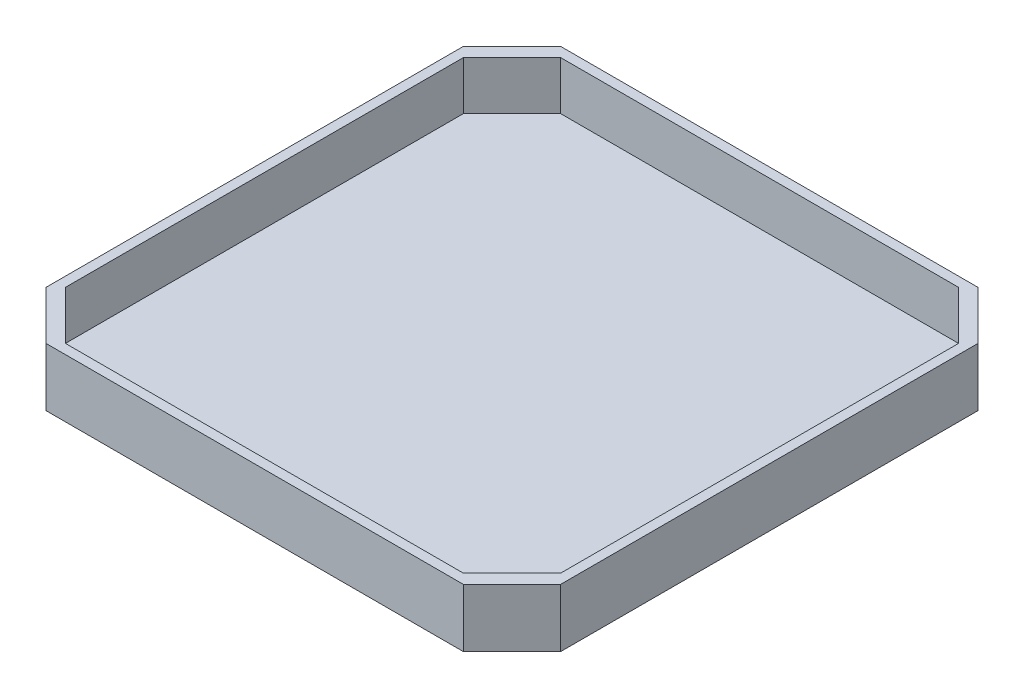
SolidWorks part; units mm, degrees
material "PLA Black"
ref_plane "Front" through (0, 0, 0) normal (0, 0, 1) x (1, 0, 0)
ref_plane "Top" through (0, 0, 0) normal (0, 1, 0) x (1, 0, 0)
ref_plane "Right" through (0, 0, 0) normal (1, 0, 0) x (0, 0, -1)
sketch "Sketch1" plane through (0, 0, 0) normal (0, 1, 0) x (1, 0, 0)
  line L0 (0, 53) -> (0, -53) construction
  line L1 (-53, 53) -> (53, 53)
  line L2 (-53, 53) -> (-53, -53)
  line L3 (-53, -53) -> (53, -53)
  line L4 (53, 53) -> (53, -53)
  dimension "D1" = 106
extrude "Boss-Extrude1" add sketch "Sketch1" along normal blind 2
sketch "Sketch2" plane through (0, 2, 0) normal (0, 1, 0) x (1, 0, 0)
  line L0 (-51, 51) -> (-51, -51)
  line L1 (-51, -51) -> (51, -51)
  line L2 (51, -51) -> (51, 51)
  line L3 (51, 51) -> (-51, 51)
  line L8 (-53, 53) -> (-53, -53)
  line L9 (-53, -53) -> (53, -53)
  line L10 (53, -53) -> (53, 53)
  line L11 (53, 53) -> (-53, 53)
  line L12 (-53, 53) -> (-53, -53)
  line L13 (-53, -53) -> (53, -53)
  line L14 (53, -53) -> (53, 53)
  line L15 (53, 53) -> (-53, 53)
  dimension "D1" = 0
  dimension "D2" = 2
extrude "Boss-Extrude2" add sketch "Sketch2" along normal blind 10
chamfer "Chamfer1" distance 10 angle 45 8 edges at (-51, 7, 51) (51, 7, 51) (53, 6, -53) (-53, 6, -53) (53, 6, 53) (51, 7, -51) (-51, 7, -51) (-53, 6, 53)
